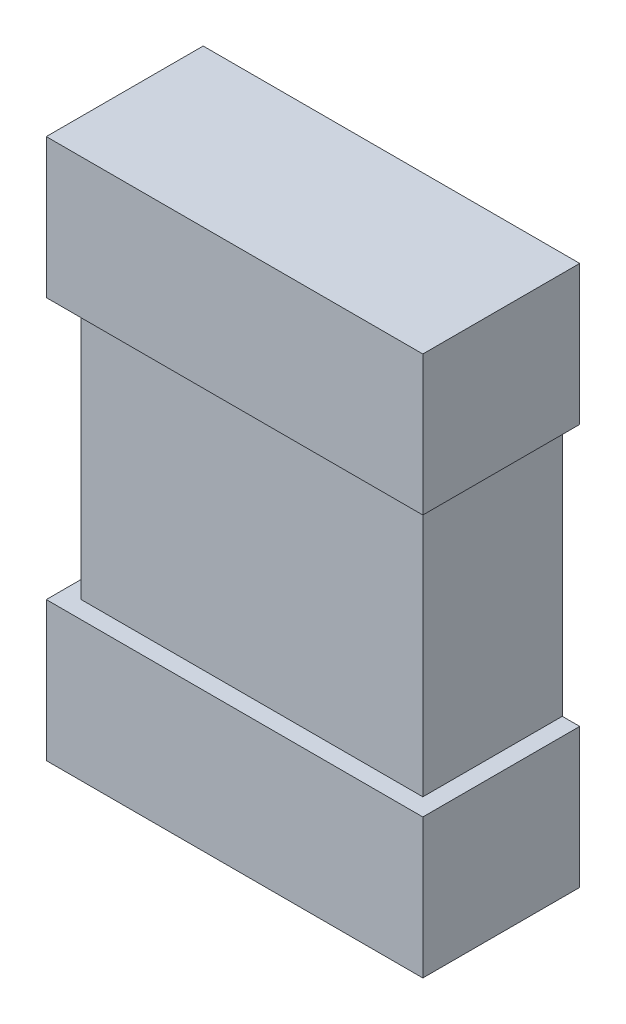
SolidWorks part; units mm, degrees
ref_plane "Front" through (0, 0, 0) normal (0, 0, 1) x (1, 0, 0)
ref_plane "Top" through (0, 0, 0) normal (0, 1, 0) x (1, 0, 0)
ref_plane "Right" through (0, 0, 0) normal (1, 0, 0) x (0, 0, -1)
sketch "COMPONENT_OUTLINE" plane through (0, 0, 0) normal (0, 0, 1) x (1, 0, 0)
  line L0 (-0.54, -0.775) -> (0.54, -0.775)
  line L1 (0.54, -0.775) -> (0.54, 0.775)
  line L2 (0.54, 0.775) -> (-0.54, 0.775)
  line L3 (-0.54, 0.775) -> (-0.54, -0.775)
extrude "Extrude1" add sketch "COMPONENT_OUTLINE" along normal blind 0.45
sketch "Sketch2" plane through (0, 0, 0.45) normal (0, 0, 1) x (1, 0, 0)
  line L6 (-0.54, -0.375) -> (0.54, -0.375)
  line L7 (-0.54, -0.375) -> (-0.49, -0.375)
  line L8 (-0.49, 0.725) -> (-0.49, -0.725)
  line L9 (-0.49, -0.725) -> (0.49, -0.725)
  line L10 (0.49, -0.725) -> (0.49, 0.725)
  line L11 (0.49, 0.725) -> (-0.49, 0.725)
  line L12 (-0.49, 0.375) -> (-0.49, -0.375)
  line L14 (0.49, -0.375) -> (0.49, 0.375)
  line L16 (0.49, -0.375) -> (0.54, -0.375)
  line L17 (0.54, 0.375) -> (-0.54, 0.375)
  line L18 (0.54, 0.375) -> (0.49, 0.375)
  line L19 (-0.49, 0.375) -> (-0.54, 0.375)
  line L22 (-0.54, 0.775) -> (-0.54, -0.775)
  line L23 (-0.54, -0.775) -> (0.54, -0.775)
  line L24 (0.54, -0.775) -> (0.54, 0.775)
  line L25 (0.54, 0.775) -> (-0.54, 0.775)
  line L26 (-0.54, 0.375) -> (-0.54, -0.375)
  line L28 (0.54, -0.375) -> (0.54, 0.375)
  dimension "D1" = 0.05
  dimension "D2" = 0.4
  dimension "D3" = 0.4
  dimension "D4" = 0
extrude "Cut-Extrude1" cut sketch "Sketch2" against normal through all
sketch "Sketch3" plane through (0.49, 0, 0) normal (1, 0, 0) x (0, 0, -1)
  line L2 (-0.4, 0.375) -> (-0.4, -0.375)
  line L3 (-0.4, 0.375) -> (-0.4, -0.375)
  line L7 (-0.45, 0.375) -> (-0.45, -0.375)
  line L8 (-0.45, -0.375) -> (0, -0.375)
  line L9 (0, -0.375) -> (0, 0.375)
  line L10 (0, 0.375) -> (-0.45, 0.375)
  line L11 (-0.45, 0.375) -> (-0.45, -0.375)
  line L12 (-0.45, -0.375) -> (-0.4, -0.375)
  line L14 (-0.4, 0.375) -> (-0.45, 0.375)
  dimension "D1" = 0.05
  dimension "D2" = 0
extrude "Cut-Extrude2" cut sketch "Sketch3" against normal through all
